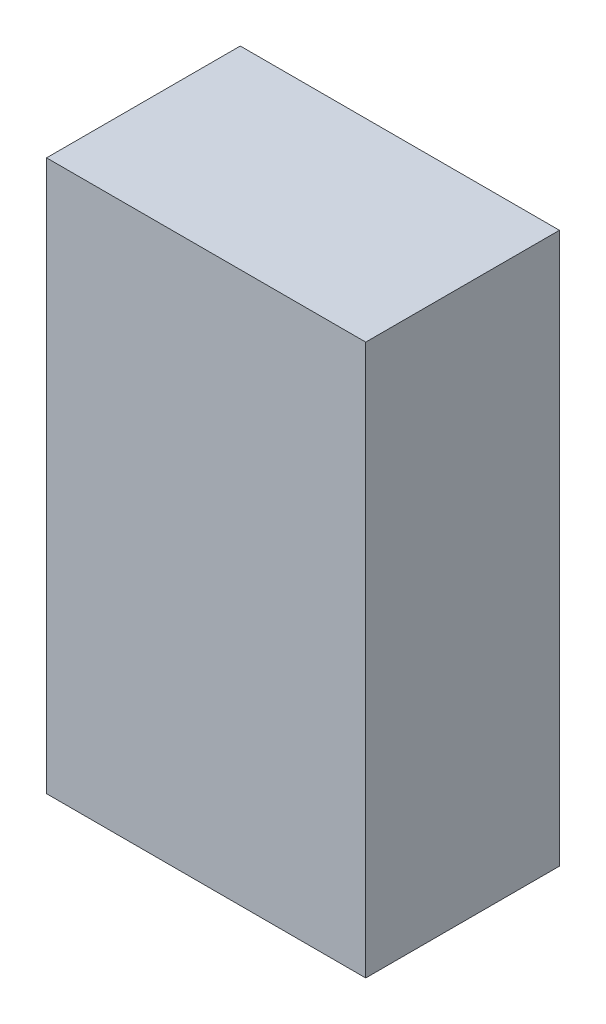
SolidWorks part; units mm, degrees
ref_plane "Front Plane" through (0, 0, 0) normal (0, 0, 1) x (1, 0, 0)
ref_plane "Top Plane" through (0, 0, 0) normal (0, 1, 0) x (1, 0, 0)
ref_plane "Right Plane" through (0, 0, 0) normal (1, 0, 0) x (0, 0, -1)
sketch "Sketch1" plane through (0, 0, 0) normal (0, 1, 0) x (1, 0, 0)
  line L1 (-39.5931, 28.5527) -> (34.0094, 28.5527)
  line L2 (-39.5931, 28.5527) -> (-39.5931, -16.1164)
  line L3 (-39.5931, -16.1164) -> (34.0094, -16.1164)
  line L4 (34.0094, 28.5527) -> (34.0094, -16.1164)
extrude "Boss-Extrude1" add sketch "Sketch1" along normal blind 127
